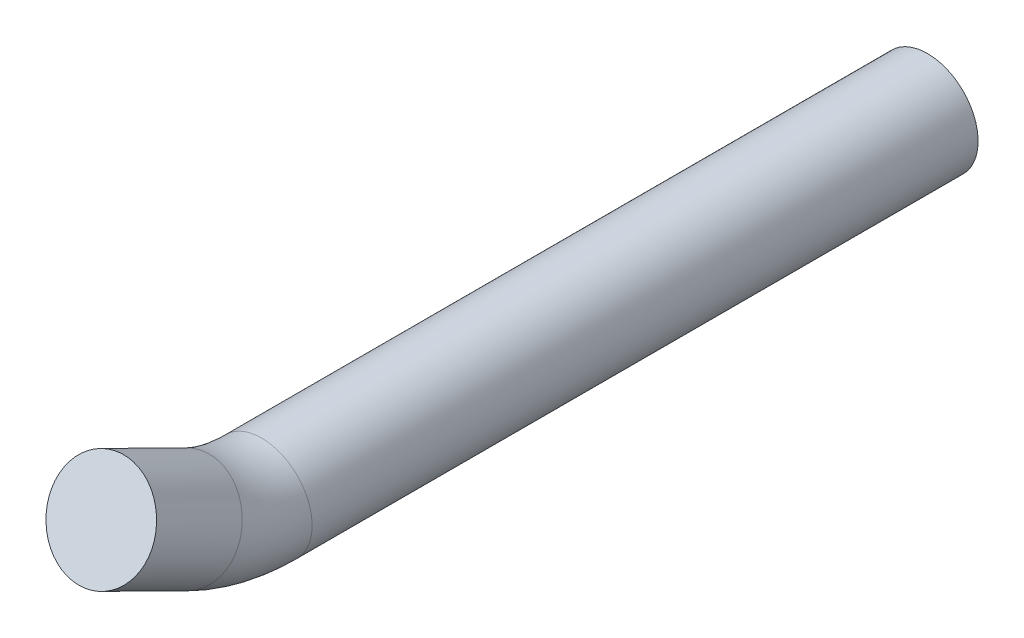
SolidWorks part; units mm, degrees
ref_plane "Alzado" through (0, 0, 0) normal (0, 0, 1) x (1, 0, 0)
ref_plane "Planta" through (0, 0, 0) normal (0, 1, 0) x (1, 0, 0)
ref_plane "Vista lateral" through (0, 0, 0) normal (1, 0, 0) x (0, 0, -1)
sketch "Croquis1" plane through (0, 0, 0) normal (0, 0, 1) x (1, 0, 0)
  circle A0 centre (0, 0) radius 15
  dimension "D1" = 30
extrude "Saliente-Extruir1" add sketch "Croquis1" along normal blind 170
sketch3d "Croquis3D3"
  line L0 (0, 0, 170) -> (0, 0, 177.488)
  line L1 (0, 0, 170) -> (0, 0, 0) construction
  line L3 (0, 5.1733, 199.6368) -> (0, 17.719, 225.0279)
  arc A0 (0, 0, 177.488) -> (0, 5.1733, 199.6368) centre (0, 50, 177.488) ccw
  point P6 (0, 0, 210.676)
  point P7 (0, 0, 240)
  point P8 (0, 43.7206, 332.7944)
  point P9 (0, 0, 208.2074)
  point P10 (0, 0, 200.2351)
  point P11 (0, 0, 189.1666)
  point P12 (0, 0, 272.6299)
  point P13 (0, 0, 216.8915)
  point P14 (-50, 50, 177.488)
  dimension "D1" = 70
  dimension "D2" = 40
  dimension "D3" = 50
sketch "Croquis2" plane through (0, 0, 170) normal (0, 0, 1) x (1, 0, 0)
  circle A0 centre (0, 0) radius 15
sweep "Barrer1" add profiles "Croquis2" path "Croquis3D3"
sketch "Croquis3" plane through (0, 0, 0) normal (0, 0, -1) x (-1, 0, 0)
  circle A0 centre (0, 0) radius 15
extrude "Saliente-Extruir2" add sketch "Croquis3" along normal blind 20
